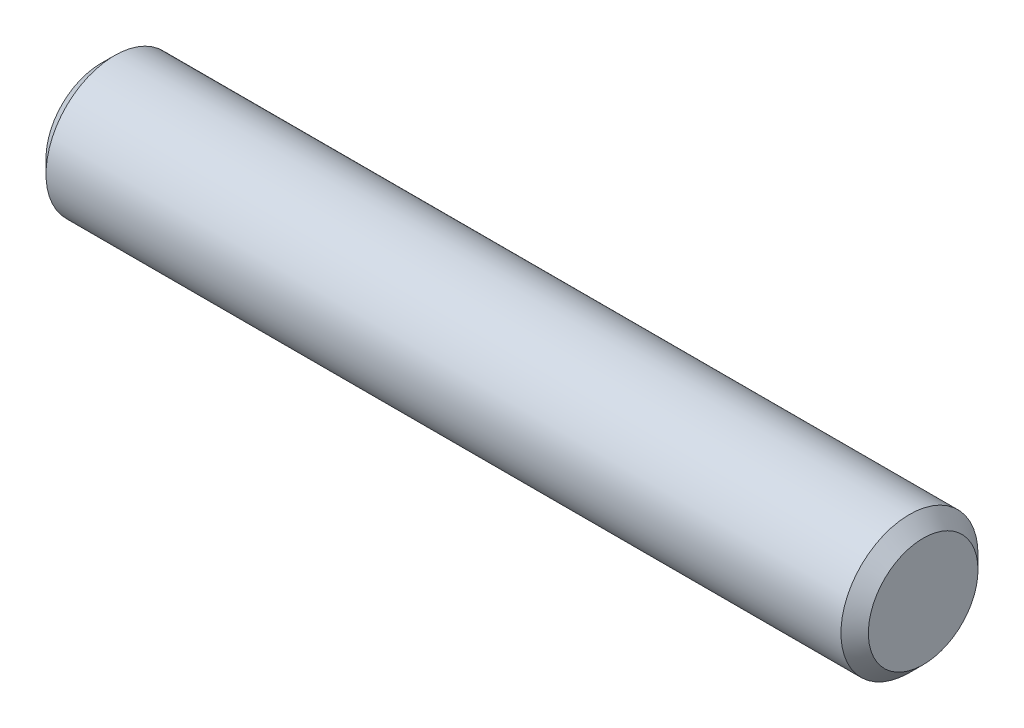
SolidWorks part; units mm, degrees
material "A-Glass Fiber"
ref_plane "Front" through (0, 0, 0) normal (0, 0, 1) x (1, 0, 0)
ref_plane "Top" through (0, 0, 0) normal (0, 1, 0) x (1, 0, 0)
ref_plane "Right" through (0, 0, 0) normal (1, 0, 0) x (0, 0, -1)
sketch "Sketch1" plane through (0, 0, 0) normal (0, 0, 1) x (1, 0, 0)
  line L0 (-9.525, 0) -> (9.525, 0) construction
  line L1 (9.525, 1.5875) -> (9.525, -1.5875) construction
  line L2 (-9.525, 1.5875) -> (-9.525, -1.5875) construction
  dimension "Length" = 19.05
  dimension "Diameter" = 3.175
sketch "Sketch2" plane through (0, 0, 0) normal (1, 0, 0) x (0, 0, -1)
  circle A0 centre (0, 0) radius 1.5875
extrude "Extrude1" add sketch "Sketch2" against normal up to vertex (9.525 mm away) and the other way up to vertex (9.525 mm away) up to point (-9.525, 1.5875, 0) other way up to point (9.525, 1.5875, 0)
chamfer "Chamfer1" distance 0.3175 angle 45 2 edges at (9.525, 0, -1.5875) (-9.525, 0, -1.5875)
equation "\"D1@Chamfer1\" = \"Diameter@Sketch1\"*.1"
